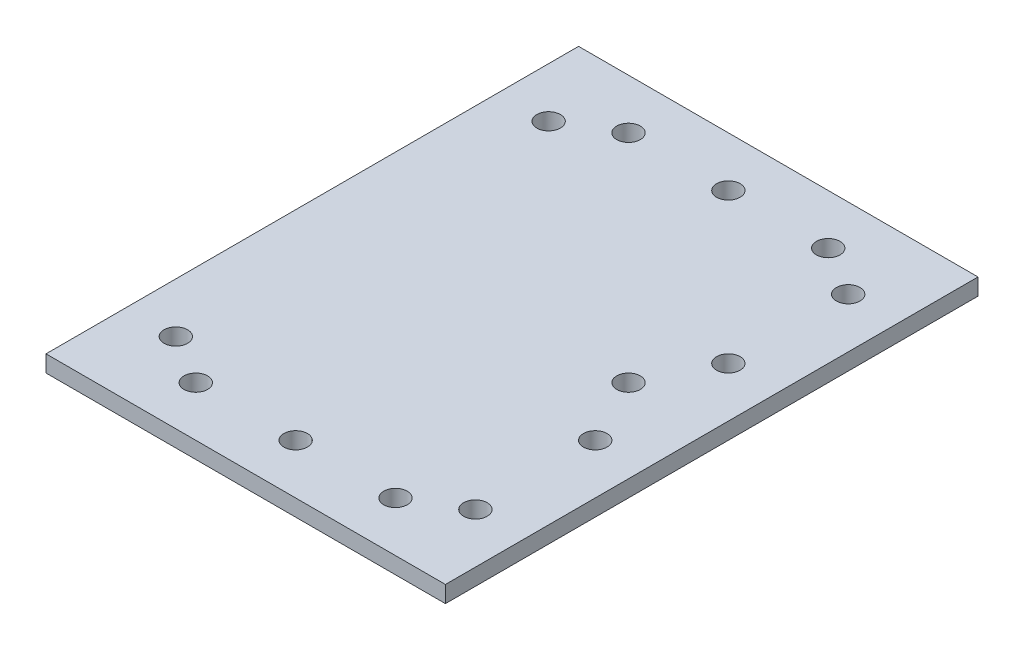
SolidWorks part; units mm, degrees
ref_plane "Front Plane" through (0, 0, 0) normal (0, 0, 1) x (1, 0, 0)
ref_plane "Top Plane" through (0, 0, 0) normal (0, 1, 0) x (1, 0, 0)
ref_plane "Right Plane" through (0, 0, 0) normal (1, 0, 0) x (0, 0, -1)
sketch "Sketch1" plane through (0, 0, 0) normal (0, 1, 0) x (1, 0, 0)
  line L0 (-19.05, -41.275) -> (19.05, -41.275) construction
  line L1 (38.1, 50.8) -> (-38.1, 50.8)
  line L2 (38.1, 50.8) -> (38.1, -50.8)
  line L3 (38.1, -50.8) -> (-38.1, -50.8)
  line L4 (-38.1, 50.8) -> (-38.1, -50.8)
  line L5 (38.1, 50.8) -> (-38.1, -50.8) construction
  line L6 (38.1, -50.8) -> (-38.1, 50.8) construction
  line L7 (0, 0) -> (0, -41.275) construction
  line L8 (28.575, -35.56) -> (-28.575, -35.56) construction
  line L9 (0, 0) -> (38.1, 0) construction
  line L10 (28.575, 12.7) -> (28.575, 0) construction
  line L11 (28.575, 0) -> (28.575, -12.7) construction
  circle A0 centre (-19.05, -41.275) radius 2.25
  circle A1 centre (19.05, -41.275) radius 2.25
  circle A2 centre (28.575, -35.56) radius 2.25
  circle A3 centre (-28.575, -35.56) radius 2.25
  circle A4 centre (28.575, 35.56) radius 2.25
  circle A5 centre (19.05, 41.275) radius 2.25
  circle A6 centre (-28.575, 35.56) radius 2.25
  circle A7 centre (-19.05, 41.275) radius 2.25
  circle A8 centre (0, -41.275) radius 2.25
  circle A9 centre (0, 41.275) radius 2.25
  circle A12 centre (28.575, 12.7) radius 2.25
  circle A13 centre (28.575, -12.7) radius 2.25
  circle A14 centre (22.23, 0) radius 2.25
  point P0 (0, 0)
  point P16 (0, -35.56)
  dimension "D3" = 9.525
  dimension "D5" = 4.5
  dimension "D8" = 12.7
  dimension "D9" = 12.69
  dimension "D1" = 101.6
  dimension "D2" = 76.2
  dimension "D4" = 9.525
  dimension "D6" = 19.05
  dimension "D7" = 15.24
extrude "Boss-Extrude1" add sketch "Sketch1" along normal blind 3.175
